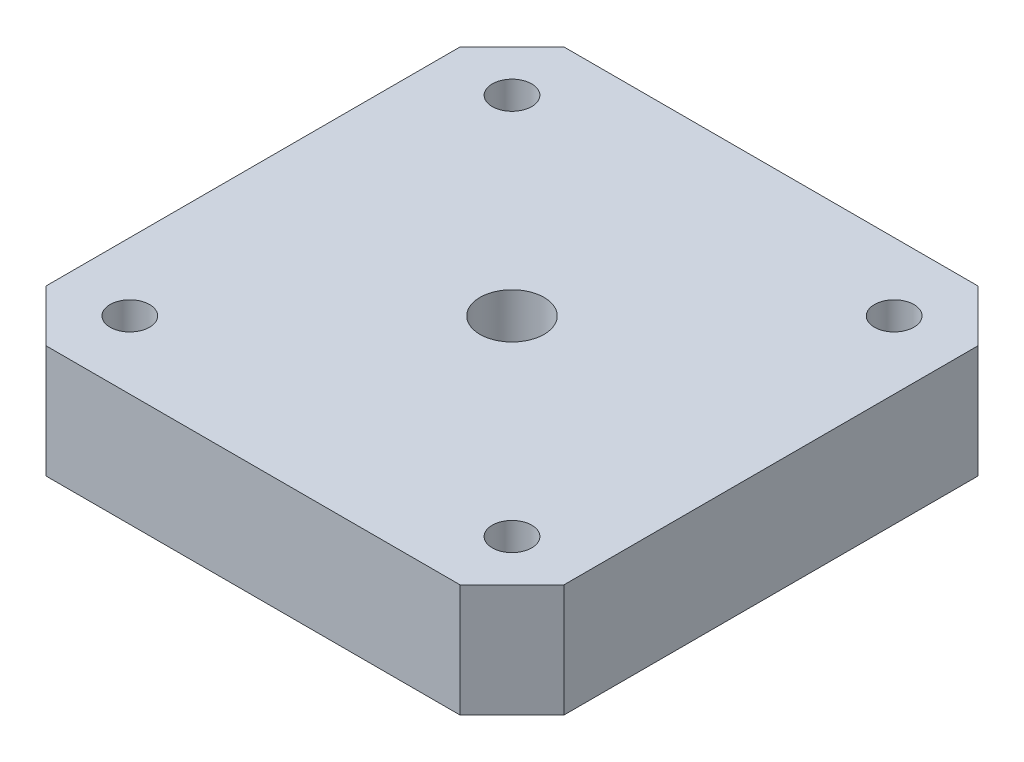
SolidWorks part; units mm, degrees
ref_plane "前视基准面" through (0, 0, 0) normal (0, 0, 1) x (1, 0, 0)
ref_plane "上视基准面" through (0, 0, 0) normal (0, 1, 0) x (1, 0, 0)
ref_plane "右视基准面" through (0, 0, 0) normal (1, 0, 0) x (0, 0, -1)
other "Configuration Table"
sketch "草图1" plane through (0, 0, 0) normal (0, 1, 0) x (1, 0, 0)
  line L1 (-21, -21) -> (21, -21)
  line L2 (-21, -21) -> (-21, 21)
  line L3 (-21, 21) -> (21, 21)
  line L4 (21, -21) -> (21, 21)
  line L5 (-21, -21) -> (21, 21) construction
  line L6 (-21, 21) -> (21, -21) construction
  circle A0 centre (-15.5, 15.5) radius 1.6
  circle A1 centre (15.5, 15.5) radius 1.6
  circle A2 centre (15.5, -15.5) radius 1.6
  circle A3 centre (-15.5, -15.5) radius 1.6
  circle A4 centre (0, 0) radius 2.6
  point P0 (0, 0)
  point P17 (0, 0)
  dimension "D3" = 4
  dimension "D4" = 31
  dimension "D5" = 3.2
  dimension "D6" = 5.2
  dimension "D1" = 42
  dimension "D2" = 42
extrude "凸台-拉伸1" add sketch "草图1" along normal blind 9.15
sketch "草图2" plane through (0, 0, 0) normal (0, -1, 0) x (1, 0, 0)
  circle A0 centre (0, 0) radius 5.15
  dimension "D1" = 10.3
extrude "切除-拉伸1" cut sketch "草图2" against normal blind 0.6
chamfer "倒角1" distance 4.2 angle 45 4 edges at (-21, 4.575, -21) (-21, 4.575, 21) (21, 4.575, -21) (21, 4.575, 21)
sketch "草图3" plane through (0, 0.6, 0) normal (0, -1, 0) x (1, 0, 0)
  circle A0 centre (0, 0) radius 4.6
  dimension "D1" = 9.2
extrude "切除-拉伸2" cut sketch "草图3" against normal blind 3
